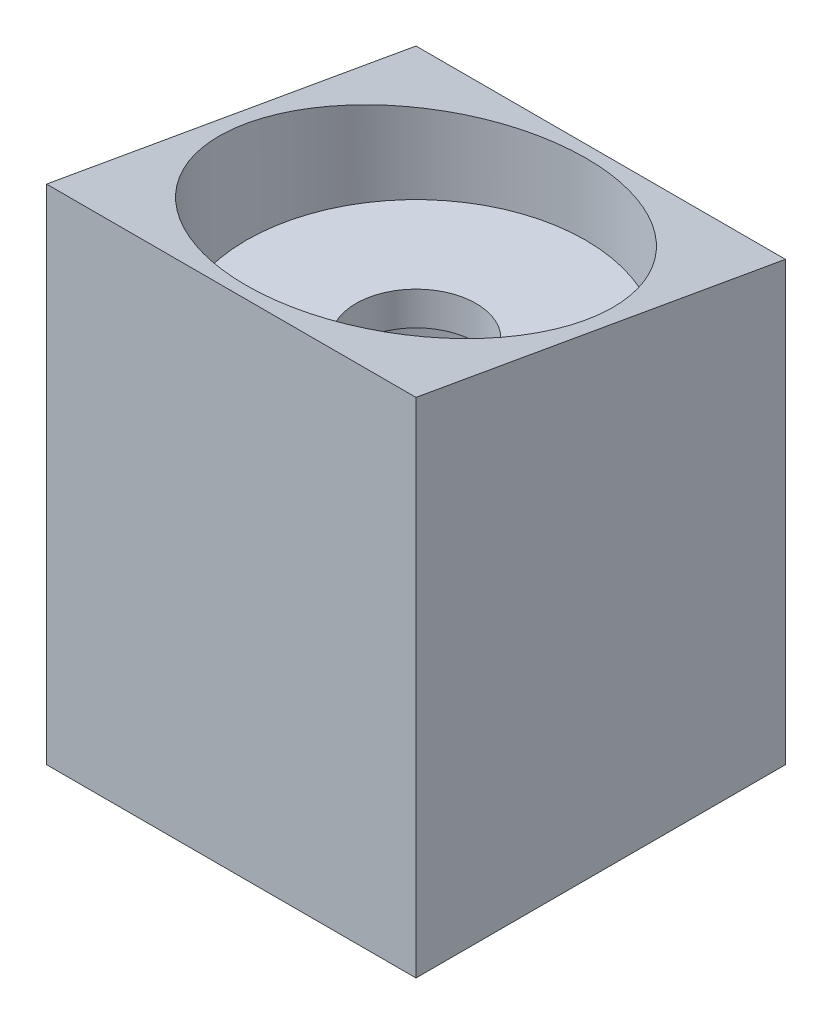
SolidWorks part; units mm, degrees
ref_plane "Front Plane" through (0, 0, 0) normal (0, 0, 1) x (1, 0, 0)
ref_plane "Top Plane" through (0, 0, 0) normal (0, 1, 0) x (1, 0, 0)
ref_plane "Right Plane" through (0, 0, 0) normal (1, 0, 0) x (0, 0, -1)
sketch "Sketch2" plane through (0, 0, 0) normal (0, 1, 0) x (1, 0, 0)
  circle A0 centre (0, 0) radius 10.1
  circle A1 centre (0, 0) radius 3.575
  dimension "D1" = 20.2
  dimension "D2" = 7.15
extrude "Boss-Extrude1" add sketch "Sketch2" along normal blind 2
sketch "Sketch3" plane through (0, 2, 0) normal (0, 1, 0) x (1, 0, 0)
  line L4 (0, 10.1) -> (0, -10.1) construction
  line L8 (-11, 11) -> (11, 11)
  line L9 (-11, 11) -> (-11, -11)
  line L10 (-11, -11) -> (11, -11)
  line L11 (11, 11) -> (11, -11)
  line L12 (-11, 11) -> (11, -11) construction
  line L13 (-11, -11) -> (11, 11) construction
  circle A0 centre (0, 0) radius 10.1 construction
  circle A3 centre (0, 0) radius 10.125
  point P0 (0, 0)
  dimension "D3" = 20.25
  dimension "D1" = 22
  dimension "D2" = 22
extrude "Boss-Extrude2" add sketch "Sketch3" along normal blind 8 and the other way blind 22
sketch "Sketch5" plane through (0, -20, 0) normal (0, -1, 0) x (-1, 0, 0)
  line L0 (11, -11) -> (9.25, -11) construction
  line L1 (11, -11) -> (-11, -11) construction
  line L2 (9.25, -11) -> (9.25, -9) construction
  line L3 (0, -11) -> (0, 11) construction
  line L4 (-11, 11) -> (11, 11) construction
  line L5 (11, 0) -> (-11, 0) construction
  line L6 (11, 11) -> (11, -11) construction
  line L7 (-11, -11) -> (-11, 11) construction
  circle A0 centre (9.25, -9) radius 0.985
  circle A1 centre (9.25, 9) radius 0.985
  circle A2 centre (-9.25, 9) radius 0.985
  circle A3 centre (-9.25, -9) radius 0.985
  dimension "D1" = 1.97
  dimension "D2" = 1.75
  dimension "D3" = 2
extrude "Cut-Extrude2" cut sketch "Sketch5" against normal blind 6
sketch "Sketch6" plane through (11, 0, 0) normal (1, 0, 0) x (0, 0, -1)
  line L0 (11, 6.0629) -> (-11, 6.0629) construction
  line L1 (11, -20) -> (11, 10) construction
  line L3 (-11, -20) -> (-11, 10) construction
  line L4 (11, 6.0629) -> (-11, 9.9421)
  line L5 (11, 6.0629) -> (11, 10)
  line L6 (11, 10) -> (-11, 10)
  line L7 (-11, 10) -> (-11, 9.9421)
  dimension "D1" = 10
extrude "Cut-Extrude3" cut sketch "Sketch6" against normal through all contours L7 L4 L5 L6
